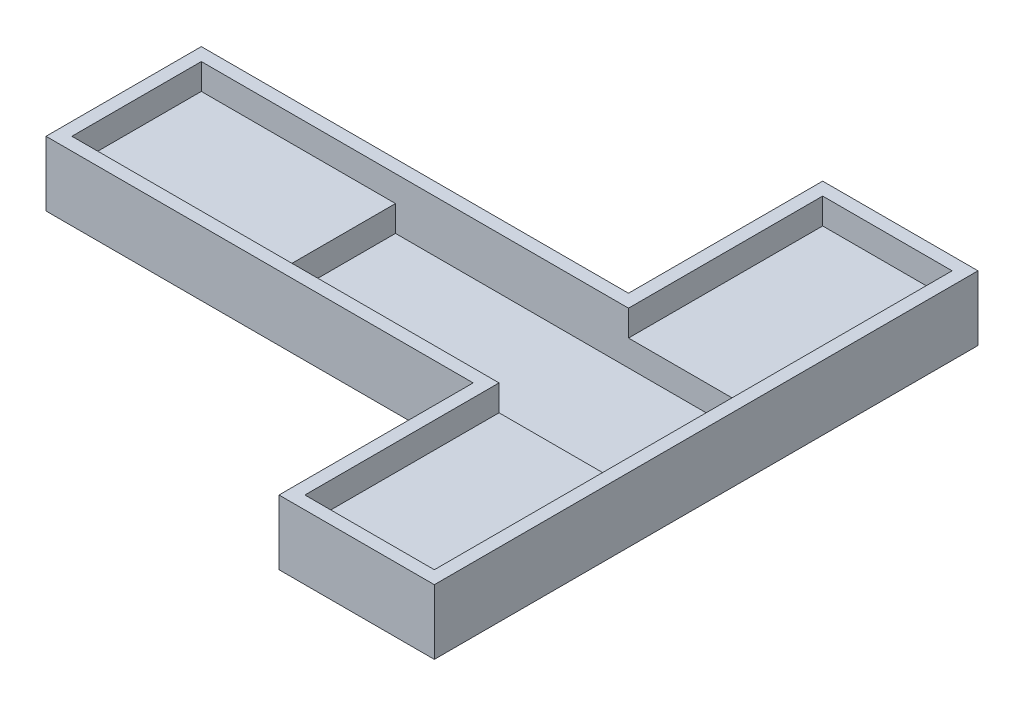
SolidWorks part; units mm, degrees
ref_plane "前视基准面" through (0, 0, 0) normal (0, 0, 1) x (1, 0, 0)
ref_plane "上视基准面" through (0, 0, 0) normal (0, 1, 0) x (1, 0, 0)
ref_plane "右视基准面" through (0, 0, 0) normal (1, 0, 0) x (0, 0, -1)
other "Configuration Table"
sketch "草图1" plane through (0, 0, 0) normal (0, 1, 0) x (1, 0, 0)
  line L1 (-14, -5) -> (14, -5)
  line L2 (-14, -5) -> (-14, 5)
  line L3 (-14, 5) -> (14, 5)
  line L4 (14, -5) -> (14, 5)
  line L5 (-14, -5) -> (14, 5) construction
  line L6 (-14, 5) -> (14, -5) construction
  line L7 (14, -5) -> (4, -5)
  line L8 (14, -5) -> (14, -20)
  line L9 (14, -20) -> (4, -20)
  line L10 (4, -5) -> (4, -20)
  line L11 (14, 5) -> (4, 5)
  line L12 (14, 5) -> (14, 20)
  line L13 (14, 20) -> (4, 20)
  line L14 (4, 5) -> (4, 20)
  line L15 (-14, 5) -> (-29, 5)
  line L16 (-14, 5) -> (-14, -5)
  line L17 (-14, -5) -> (-29, -5)
  line L18 (-29, 5) -> (-29, -5)
  point P0 (0, 0)
  dimension "D1" = 28
  dimension "D2" = 10
  dimension "D3" = 10
  dimension "D4" = 10
  dimension "D5" = 15
  dimension "D6" = 15
  dimension "D7" = 15
sketch "草图2" plane through (0, 0, 0) normal (0, 1, 0) x (1, 0, 0)
  line L1 (-29, 5) -> (14, 5)
  line L2 (-29, 5) -> (-29, -5)
  line L3 (-29, -5) -> (14, -5)
  line L4 (14, 5) -> (14, -5)
  line L5 (14, -20) -> (4, -20)
  line L6 (14, -20) -> (14, -5)
  line L7 (14, -5) -> (4, -5)
  line L8 (4, -20) -> (4, -5)
  line L9 (4, 5) -> (14, 5)
  line L10 (4, 5) -> (4, 20)
  line L11 (4, 20) -> (14, 20)
  line L12 (14, 5) -> (14, 20)
extrude "凸台-拉伸1" add sketch "草图2" along normal blind 1 contours L4 L1 L2 L3 | L1 L12 L11 L10 | L8 L5 L6 L3
sketch "草图3" plane through (0, 1, 0) normal (0, 1, 0) x (1, 0, 0)
  line L0 (15, -21) -> (15, 21)
  line L1 (15, 21) -> (3, 21)
  line L2 (3, 21) -> (3, 6)
  line L3 (3, 6) -> (-30, 6)
  line L4 (-30, 6) -> (-30, -6)
  line L5 (-30, -6) -> (3, -6)
  line L6 (3, -6) -> (3, -21)
  line L7 (3, -21) -> (15, -21)
  line L8 (14, -20) -> (14, 20)
  line L9 (14, 20) -> (4, 20)
  line L10 (4, 20) -> (4, 5)
  line L11 (4, 5) -> (-29, 5)
  line L12 (-29, 5) -> (-29, -5)
  line L13 (-29, -5) -> (4, -5)
  line L14 (4, -5) -> (4, -20)
  line L15 (4, -20) -> (14, -20)
  line L16 (14, -20) -> (14, 20)
  line L17 (14, 20) -> (4, 20)
  line L18 (4, 20) -> (4, 5)
  line L19 (4, 5) -> (-29, 5)
  line L20 (-29, 5) -> (-29, -5)
  line L21 (-29, -5) -> (4, -5)
  line L22 (4, -5) -> (4, -20)
  line L23 (4, -20) -> (14, -20)
  dimension "D1" = 0
  dimension "D2" = 1
extrude "凸台-拉伸2" add sketch "草图3" along normal blind 4 and the other way blind 1
sketch "草图4" plane through (0, 1, 0) normal (0, 1, 0) x (1, 0, 0)
  line L1 (-29, 5) -> (-14, 5)
  line L2 (-29, 5) -> (-29, -5)
  line L3 (-29, -5) -> (-14, -5)
  line L4 (-14, 5) -> (-14, -5)
  line L5 (4, 5) -> (14, 5)
  line L6 (4, 5) -> (4, 20)
  line L7 (4, 20) -> (14, 20)
  line L8 (14, 5) -> (14, 20)
  line L9 (4, -5) -> (14, -5)
  line L10 (4, -5) -> (4, -20)
  line L11 (4, -20) -> (14, -20)
  line L12 (14, -5) -> (14, -20)
extrude "凸台-拉伸3" add sketch "草图4" along normal blind 2
